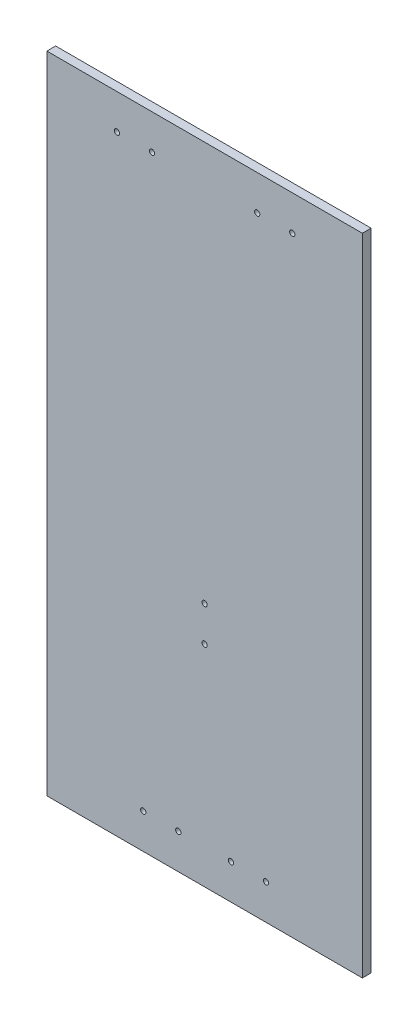
SolidWorks part; units mm, degrees
ref_plane "Alzado" through (0, 0, 0) normal (0, 0, 1) x (1, 0, 0)
ref_plane "Planta" through (0, 0, 0) normal (0, 1, 0) x (1, 0, 0)
ref_plane "Vista lateral" through (0, 0, 0) normal (1, 0, 0) x (0, 0, -1)
sketch "Croquis1" plane through (0, 0, 0) normal (0, 0, 1) x (1, 0, 0)
  line L0 (0, 184) -> (0, -184) construction
  line L1 (-90, -184) -> (90, -184)
  line L2 (-90, -184) -> (-90, 184)
  line L3 (-90, 184) -> (90, 184)
  line L4 (90, -184) -> (90, 184)
  line L5 (-90, -184) -> (90, 184) construction
  line L6 (-90, 184) -> (90, -184) construction
  circle A0 centre (15, -164) radius 1.5
  circle A1 centre (35, -164) radius 1.5
  circle A2 centre (-35, -164) radius 1.5
  circle A3 centre (-15, -164) radius 1.5
  circle A4 centre (30, 164) radius 1.5
  circle A5 centre (50, 164) radius 1.5
  circle A6 centre (-50, 164) radius 1.5
  circle A7 centre (-30, 164) radius 1.5
  circle A8 centre (0, -64) radius 1.5
  circle A9 centre (0, -44) radius 1.5
  point P0 (0, 0)
  dimension "D5" = 3
  dimension "D6" = 3
  dimension "D10" = 3
  dimension "D11" = 3
  dimension "D13" = 3
  dimension "D14" = 3
  dimension "D1" = 368
  dimension "D2" = 180
  dimension "D3" = 15
  dimension "D4" = 20
  dimension "D7" = 20
  dimension "D8" = 30
  dimension "D9" = 20
  dimension "D12" = 20
  dimension "D15" = 20
  dimension "D16" = 120
extrude "Saliente-Extruir1" add sketch "Croquis1" along normal blind 5
